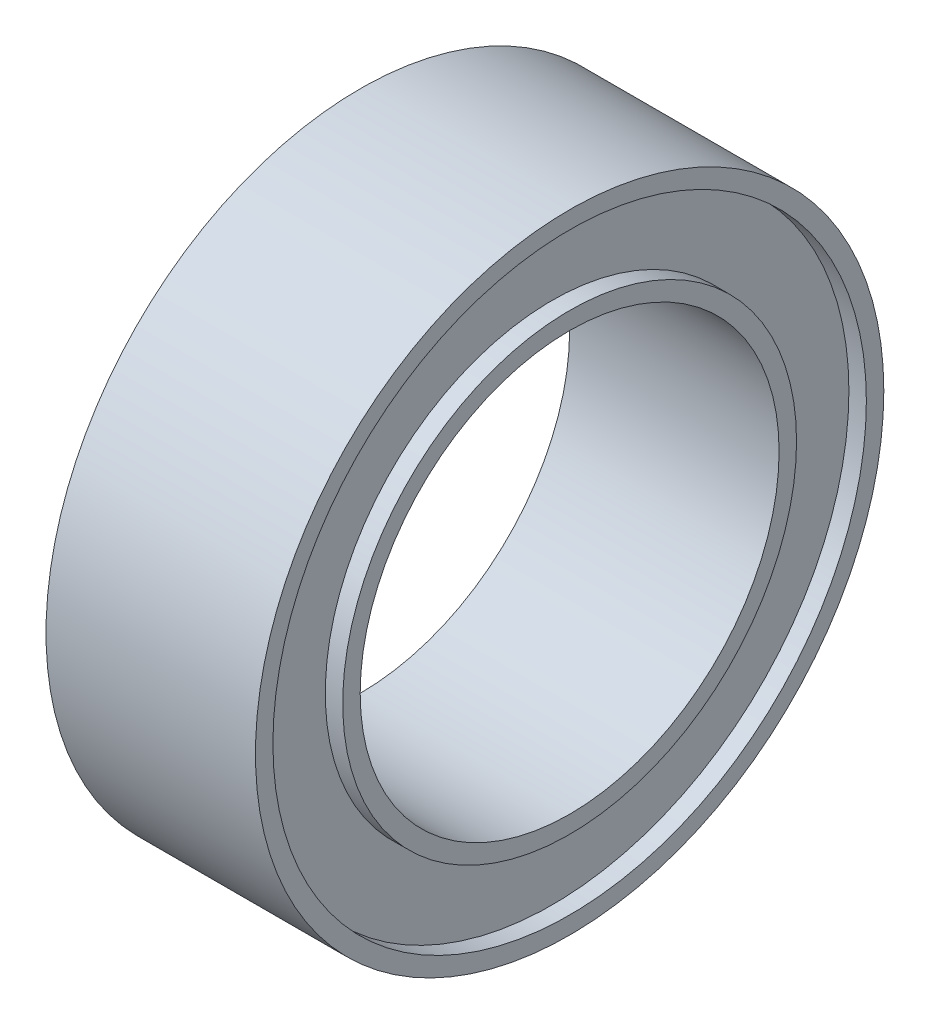
SolidWorks part; units mm, degrees
ref_plane "Front Plane" through (0, 0, 0) normal (0, 0, 1) x (1, 0, 0)
ref_plane "Top Plane" through (0, 0, 0) normal (0, 1, 0) x (1, 0, 0)
ref_plane "Right Plane" through (0, 0, 0) normal (1, 0, 0) x (0, 0, -1)
sketch "Sketch2" plane through (0, 0, 0) normal (1, 0, 0) x (0, 0, -1)
  circle A0 centre (0, 0) radius 9
extrude "Boss-Extrude1" add sketch "Sketch2" along normal mid plane 6
sketch "Sketch3" plane through (3, 0, 0) normal (1, 0, 0) x (0, 0, -1)
  circle A0 centre (0, 0) radius 6
extrude "Cut-Extrude1" cut sketch "Sketch3" against normal blind 6
sketch "Sketch4" plane through (3, 0, 0) normal (1, 0, 0) x (0, 0, -1)
  circle A0 centre (0, 0) radius 7.5
  circle A1 centre (0, 0) radius 8.5
  circle A2 centre (0, 0) radius 6.5
  dimension "D1" = 1
  dimension "D2" = 1
extrude "Cut-Extrude2" cut sketch "Sketch4" against normal blind 0.5 contours A0 A2 | A1 A0
mirror "Mirror1" about plane through (0, 0, 0) normal (1, 0, 0) of "Cut-Extrude2"
